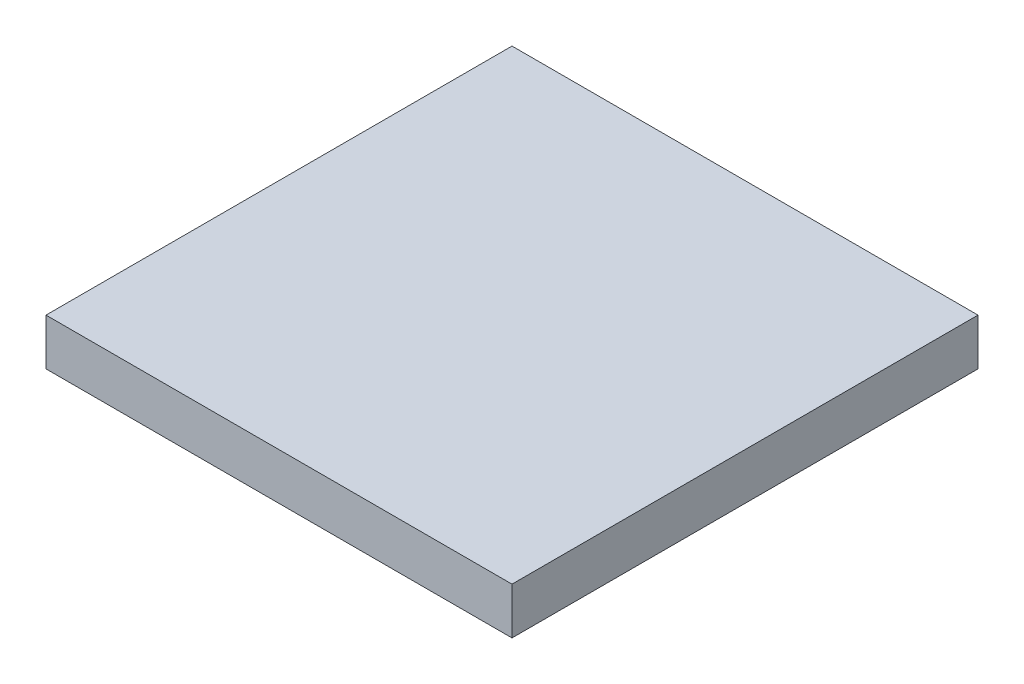
SolidWorks part; units mm, degrees
ref_plane "Front Plane" through (0, 0, 0) normal (0, 0, 1) x (1, 0, 0)
ref_plane "Top Plane" through (0, 0, 0) normal (0, 1, 0) x (1, 0, 0)
ref_plane "Right Plane" through (0, 0, 0) normal (1, 0, 0) x (0, 0, -1)
sketch "Sketch1" plane through (0, 0, 0) normal (0, 1, 0) x (1, 0, 0)
  line L1 (0, 0) -> (100, 0)
  line L2 (0, 0) -> (0, 100)
  line L3 (0, 100) -> (100, 100)
  line L4 (100, 0) -> (100, 100)
  dimension "D1" = 100
  dimension "D2" = 100
extrude "Boss-Extrude1" add sketch "Sketch1" along normal blind 10
